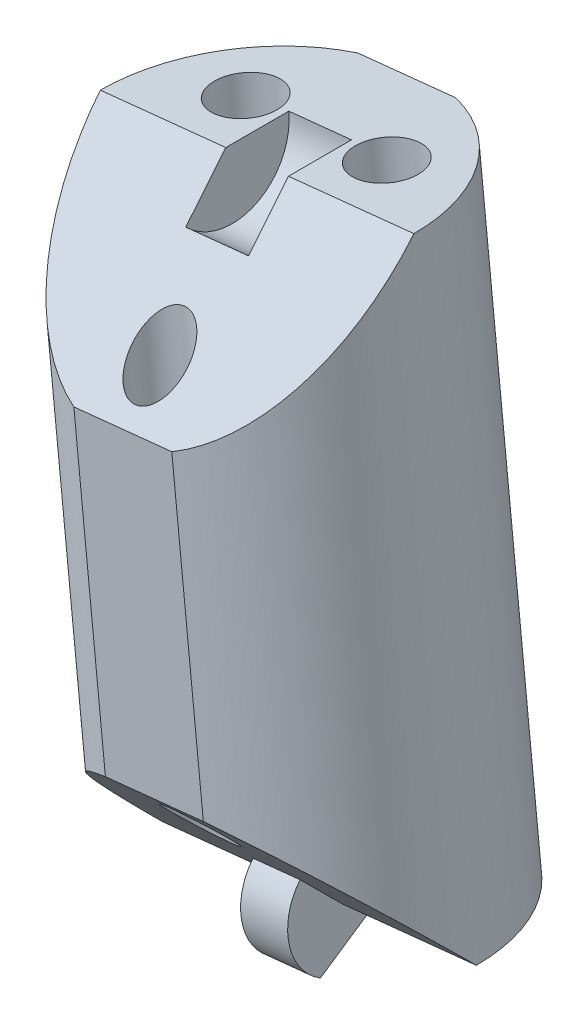
SolidWorks part; units mm, degrees
ref_plane "Front Plane" through (0, 0, 0) normal (0, 0, 1) x (1, 0, 0)
ref_plane "Top Plane" through (0, 0, 0) normal (0, 1, 0) x (1, 0, 0)
ref_plane "Right Plane" through (0, 0, 0) normal (1, 0, 0) x (0, 0, -1)
sketch "Sketch2" plane through (0, 0, 0) normal (0, 0, 1) x (1, 0, 0)
  line L0 (0, 0) -> (90, 0)
  line L1 (90, 0) -> (90, 120)
  line L2 (90, 120) -> (0, 120)
  line L3 (0, 120) -> (0, 0)
  line L4 (0, 120) -> (-10, 120)
  line L5 (-10, 120) -> (-10, 16.9491)
  line L6 (-10, 120) -> (57.5, 127)
  line L7 (57.5, 127) -> (90, 124)
  line L8 (90, 120) -> (99, 60)
  line L10 (90, 124) -> (90, 120)
  line L11 (5.9147, 0) -> (5.9147, -25)
  line L12 (5.9147, -25) -> (-4.0853, -25)
  line L13 (-4.0853, -29) -> (-4.0853, 0)
  line L14 (80, 0) -> (80, -25)
  line L15 (80, -25) -> (90, -25)
  line L16 (90, -29) -> (90, 0)
  line L17 (15.7927, 122.6748) -> (5.4776, 222.1414)
  line L18 (5.4776, 222.1414) -> (21.3923, 223.7918)
  line L19 (21.3923, 223.7918) -> (31.7073, 124.3252)
  line L20 (7.6492, 201.201) -> (23.5639, 202.8514)
  line L21 (10.9066, 169.7905) -> (26.8212, 171.441)
  line L22 (-10, 120) -> (-20.0396, 216.8108)
  line L23 (-20.0396, 216.8108) -> (-4.125, 218.4612)
  line L24 (-4.125, 218.4612) -> (5.9147, 121.6504)
  line L25 (-17.926, 196.4296) -> (-2.0114, 198.08)
  line L26 (-14.7556, 165.8578) -> (1.159, 167.5082)
  line L27 (57.5, 127) -> (46.9095, 229.1223)
  line L28 (46.9095, 229.1223) -> (30.9949, 227.4719)
  line L29 (30.9949, 227.4719) -> (41.5853, 125.3496)
  line L30 (33.2245, 205.9725) -> (49.1391, 207.6229)
  line L31 (36.5688, 173.7233) -> (52.4835, 175.3737)
  line L34 (90, 124) -> (99.1917, 223.5767)
  line L35 (99.1917, 223.5767) -> (83.2594, 225.0473)
  line L36 (83.2594, 225.0473) -> (74.0677, 125.4707)
  line L38 (81.3243, 204.0838) -> (97.2566, 202.6132)
  line L39 (78.4217, 172.6386) -> (94.354, 171.1679)
  line L40 (62.4078, 79.6749) -> (57.5, 127) construction
  line L41 (41.5853, 125.3496) -> (46.4931, 78.0244) construction
  line L42 (46.4931, 78.0244) -> (62.4078, 79.6749) construction
  line L43 (31.7073, 124.3252) -> (36.6151, 77.0001) construction
  line L44 (36.6151, 77.0001) -> (20.7005, 75.3496) construction
  line L45 (20.7005, 75.3496) -> (15.7927, 122.6748) construction
  line L46 (5.9147, 121.6504) -> (10.8224, 74.3253) construction
  line L47 (10.8224, 74.3253) -> (-5.0922, 72.6749) construction
  line L48 (-5.0922, 72.6749) -> (-10, 120) construction
  line L49 (74.0677, 125.4707) -> (69.6944, 78.0931) construction
  line L50 (69.6944, 78.0931) -> (85.7624, 78.0931) construction
  line L51 (85.7624, 78.0931) -> (90, 124) construction
  line L52 (-12.0823, 217.636) -> (10.4873, 0) construction
  line L53 (13.4349, 222.9666) -> (36.5574, 0) construction
  line L54 (38.9522, 228.2971) -> (62.6275, 0) construction
  line L55 (91.2256, 224.312) -> (70.5198, 0) construction
  line L59 (99, 60) -> (93.5277, 44.9649)
  line L60 (99, 60) -> (169.4769, 34.3485)
  line L61 (169.4769, 34.3485) -> (164.0046, 19.3134)
  line L62 (164.0046, 19.3134) -> (93.5277, 44.9649)
  line L63 (90, -2) -> (100, -2)
  line L64 (141.2862, 44.6091) -> (135.8138, 29.574)
  line L65 (99, 60) -> (55.7741, 75.7329) construction
  line L66 (55.7741, 75.7329) -> (50.3018, 60.6978) construction
  line L67 (100, -2) -> (100, -29)
  line L70 (-4.0853, -2) -> (-14.0853, -2)
  line L71 (-14.0853, -2) -> (-14.0853, -29)
  line L74 (-4.0853, 0) -> (0, 0)
  line L75 (-14.0853, -29) -> (-14.0853, -112.587)
  line L76 (-14.0853, -112.587) -> (100, -112.587)
  line L77 (100, -112.587) -> (100, -29)
  line L78 (-14.0853, -29) -> (100, -29)
  line L79 (-14.0853, -14.5) -> (100, -14.5) construction
  line L80 (31.7073, -112.587) -> (31.7073, -122.6232)
  line L81 (31.7073, -122.6232) -> (42.9573, -122.6232)
  line L82 (42.9573, -122.6232) -> (42.9573, -112.587)
  line L83 (-14.0853, -112.587) -> (-88.3667, -112.587)
  line L84 (-88.3667, -112.587) -> (-88.3667, -128.2699)
  line L85 (-88.3667, -128.2699) -> (169.4958, -128.2699)
  line L86 (169.4958, -128.2699) -> (169.4958, -112.587)
  line L87 (169.4958, -112.587) -> (100, -112.587)
  line L88 (90, 60) -> (-10, 60) construction
  line L89 (50.3018, 60.6978) -> (93.5277, 44.9649) construction
  line L90 (87.2806, 55.7521) -> (166.7408, 26.8309) construction
  line L91 (87.2806, 55.7521) -> (82.1749, 52.5336) construction
  line L92 (82.1749, 52.5336) -> (77.3257, 0) construction
  line L93 (83.1185, 56.6957) -> (86.337, 51.59) construction
  arc A0 (-10, 16.9491) -> (-4.0853, 0) centre (14.9876, 16.1624) ccw
  arc A1 (93.5277, 44.9649) -> (90, 0) centre (-126.4069, 39.5988) cw
  point P42 (41.1818, 206.7977)
  point P100 (84.7278, 54.1428)
  point P101 (84.7278, 54.1428)
  dimension "D11" = 47.3684
  dimension "D35" = 9
  dimension "D32" = 220
  dimension "D36" = 25
  dimension "D1" = 120
  dimension "D2" = 90
  dimension "D3" = 10
  dimension "D5" = 67.862
  dimension "D6" = 7
  dimension "D7" = 4
  dimension "D8" = 16
  dimension "D9" = 16
  dimension "D10" = 100
  dimension "D12" = 31.5789
  dimension "D13" = 16
  dimension "D14" = 16
  dimension "D15" = 16
  dimension "D16" = 25.7927
  dimension "D17" = 100
  dimension "D18" = 21.0526
  dimension "D19" = 31.5789
  dimension "D20" = 97.33
  dimension "D21" = 102.67
  dimension "D22" = 20.4905
  dimension "D23" = 30.7358
  dimension "D24" = 21.6147
  dimension "D25" = 32.4221
  dimension "D26" = 25
  dimension "D28" = 25
  dimension "D29" = 75
  dimension "D30" = 47.5789
  dimension "D31" = 30
  dimension "D33" = 46
  dimension "D34" = 20
  dimension "D37" = 2
  dimension "D38" = 2
  dimension "D39" = 27
  dimension "D40" = 10
  dimension "D41" = 10
  dimension "D42" = 27
  dimension "D43" = 14.5
  dimension "D44" = 127.5
ref_plane "Plane1" through (87.2806, 55.7521, 0) normal (-0.846, -0.5333, 0) x (0, 0, 1)
ref_plane "Plane2" through (82.1749, 52.5336, 0) normal (-0.0919, -0.9958, 0) x (-0.9958, 0.0919, 0)
ref_plane "Plane3" through (91.2256, 224.312, 0) normal (-0.0919, -0.9958, 0) x (-0.9958, 0.0919, 0)
ref_plane "Plane4" through (38.9522, 228.2971, 0) normal (0.1032, -0.9947, 0) x (-0.9947, -0.1032, 0)
ref_plane "Plane5" through (13.4349, 222.9666, 0) normal (0.1032, -0.9947, 0) x (-0.9947, -0.1032, 0)
ref_plane "Plane7" through (166.7408, 26.8309, 0) normal (0.9397, -0.342, 0) x (0, 0, -1)
ref_plane "Plane8" through (110.4217, -40.1902, 0) normal (0.9397, -0.342, 0) x (0, 0, -1)
ref_plane "Plane9" through (19.3664, 209.803, 0) normal (-0.0919, -0.9958, 0) x (-0.9958, 0.0919, 0)
ref_plane "Plane10" through (16.4638, 178.3578, 0) normal (-0.0919, -0.9958, 0) x (-0.9958, 0.0919, 0)
ref_plane "Plane11" through (-20.7793, 200.3721, 0) normal (0.1032, -0.9947, 0) x (-0.9947, -0.1032, 0)
ref_plane "Plane12" through (-17.435, 168.1229, 0) normal (0.1032, -0.9947, 0) x (-0.9947, -0.1032, 0)
ref_plane "Plane13" through (-20.5619, 198.2754, 0) normal (0.1032, -0.9947, 0) x (-0.9947, -0.1032, 0)
ref_plane "Plane14" through (-17.3045, 166.8649, 0) normal (0.1032, -0.9947, 0) x (-0.9947, -0.1032, 0)
ref_plane "Plane15" through (-12.0823, 217.636, 0) normal (0.1032, -0.9947, 0) x (-0.9947, -0.1032, 0)
ref_plane "Plane16" through (-20.3445, 196.1788, 0) normal (0.1032, -0.9947, 0) x (-0.9947, -0.1032, 0)
ref_plane "Plane17" through (-17.1741, 165.607, 0) normal (0.1032, -0.9947, 0) x (-0.9947, -0.1032, 0)
ref_plane "Plane18" through (12.1098, 131.1899, 0) normal (-0.0919, -0.9958, 0) x (-0.9958, 0.0919, 0)
ref_plane "Plane19" through (-12.4184, 119.7492, 0) normal (0.1032, -0.9947, 0) x (-0.9947, -0.1032, 0)
ref_plane "Plane20" through (0, 0, 0) normal (0, 0, 1) x (0.1032, -0.9947, 0)
ref_plane "Plane21" through (0, 0, 0) normal (0, 0, 1) x (-0.0919, -0.9958, 0)
ref_plane "Plane22" through (10.3758, 1.076, 0) normal (-0.9947, -0.1032, 0) x (0.1032, -0.9947, 0)
ref_plane "Plane23" through (36.1684, 3.7508, 0) normal (-0.9947, -0.1032, 0) x (0.1032, -0.9947, 0)
ref_plane "Plane24" through (61.9611, 6.4256, 0) normal (-0.9947, -0.1032, 0) x (0.1032, -0.9947, 0)
ref_plane "Plane25" through (69.924, -6.4545, 0) normal (-0.9958, 0.0919, 0) x (-0.0919, -0.9958, 0)
sketch "Sketch3" plane through (-20.3445, 196.1788, 0) normal (0.1032, -0.9947, 0) x (-0.9947, -0.1032, 0)
  line L0 (-2.4314, 0) -> (-18.4314, 0) construction
  circle A0 centre (-10.4314, 0) radius 8
  dimension "D1" = 16
extrude "Boss-Extrude1" add sketch "Sketch3" along normal blind 30.7358
sketch "Sketch4" plane through (10.3758, 1.076, 0) normal (-0.9947, -0.1032, 0) x (0.1032, -0.9947, 0)
  line L0 (-197.2309, 0) -> (-189.2309, 8)
  line L1 (-197.2309, 8) -> (-197.2309, -8) construction
  line L2 (-166.4951, 8) -> (-197.2309, 8) construction
  line L3 (-189.2309, 8) -> (-197.2309, 8)
  line L4 (-197.2309, 8) -> (-197.2309, 0)
  line L5 (-174.4951, 8) -> (-166.4951, 8)
  line L6 (-166.4951, 8) -> (-166.4951, 0)
  line L7 (-217.7214, 0) -> (1.0818, 0) construction
  line L8 (-166.4951, 0) -> (-174.4951, 8)
  dimension "D1" = 45
  dimension "D2" = 45
extrude "Cut-Extrude1" cut sketch "Sketch4" against normal through all and the other way through all
sketch "Sketch5" plane through (10.3758, 1.076, 0) normal (-0.9947, -0.1032, 0) x (0.1032, -0.9947, 0)
  line L1 (-166.4951, -2.8) -> (-164.0702, 1.4)
  line L6 (-166.4951, 0) -> (-174.4951, 8) construction
  line L11 (-166.4951, -8) -> (-166.4951, 0) construction
  line L12 (-168.475, 1.9799) -> (-166.4951, 0)
  line L13 (-166.4951, 0) -> (-166.4951, -2.8)
  arc A3 (-168.475, 1.9799) -> (-164.0702, 1.4) centre (-166.4951, 0) cw
  dimension "D2" = 2.8
  dimension "D1" = 30
  dimension "D3" = 2.8
extrude "Boss-Extrude2" add sketch "Sketch5" along normal mid plane 2.4
sketch "Sketch7" plane through (10.3758, 1.076, 0) normal (-0.9947, -0.1032, 0) x (0.1032, -0.9947, 0)
  line L6 (-197.2309, 0) -> (-197.2309, -8) construction
  line L7 (-189.2309, 8) -> (-197.2309, 0) construction
  line L8 (-194.9681, 2.2627) -> (-197.2309, 0)
  line L9 (-197.2309, 0) -> (-197.2309, -3.2)
  arc A1 (-197.2309, -3.2) -> (-194.9681, 2.2627) centre (-197.2309, 0) ccw
  dimension "D1" = 3.2
extrude "Cut-Extrude2" cut sketch "Sketch7" against normal mid plane 3.2
sketch "Sketch8" plane through (-20.3445, 196.1788, 0) normal (-0.1032, 0.9947, 0) x (0.9947, 0.1032, 0)
  line L0 (2.4314, 0) -> (18.4314, 0) construction
  circle A0 centre (10.4314, -5.5) radius 1.4
  circle A1 centre (6.8314, 3) radius 1.6
  circle A2 centre (14.0314, 3) radius 1.6
  point P9 (10.4314, 0)
  dimension "D1" = 3.2
  dimension "D2" = 3.2
  dimension "D3" = 2.8
  dimension "D4" = 3
  dimension "D5" = 5.5
  dimension "D6" = 3.6
  dimension "D7" = 3.6
  dimension "D8" = 3
extrude "Cut-Extrude3" cut sketch "Sketch8" against normal through all and the other way through all
sketch "Sketch9" plane through (-20.3445, 196.1788, 0) normal (-0.1032, 0.9947, 0) x (0.9947, 0.1032, 0)
  line L0 (7.9334, 7.6) -> (12.9294, 7.6)
  line L1 (-101.1265, 0) -> (155.3606, 0) construction
  line L2 (7.9334, -7.6) -> (12.9294, -7.6)
  arc A0 (18.4314, 0) -> (2.4314, 0) centre (10.4314, 0) ccw construction
  arc A1 (7.9334, 7.6) -> (12.9294, 7.6) centre (10.4314, 0) cw
  arc A2 (2.4314, 0) -> (18.4314, 0) centre (10.4314, 0) ccw construction
  arc A3 (7.9334, -7.6) -> (12.9294, -7.6) centre (10.4314, 0) ccw
  dimension "D1" = 7.6
  dimension "D2" = 7.6
extrude "Cut-Extrude4" cut sketch "Sketch9" against normal through all
